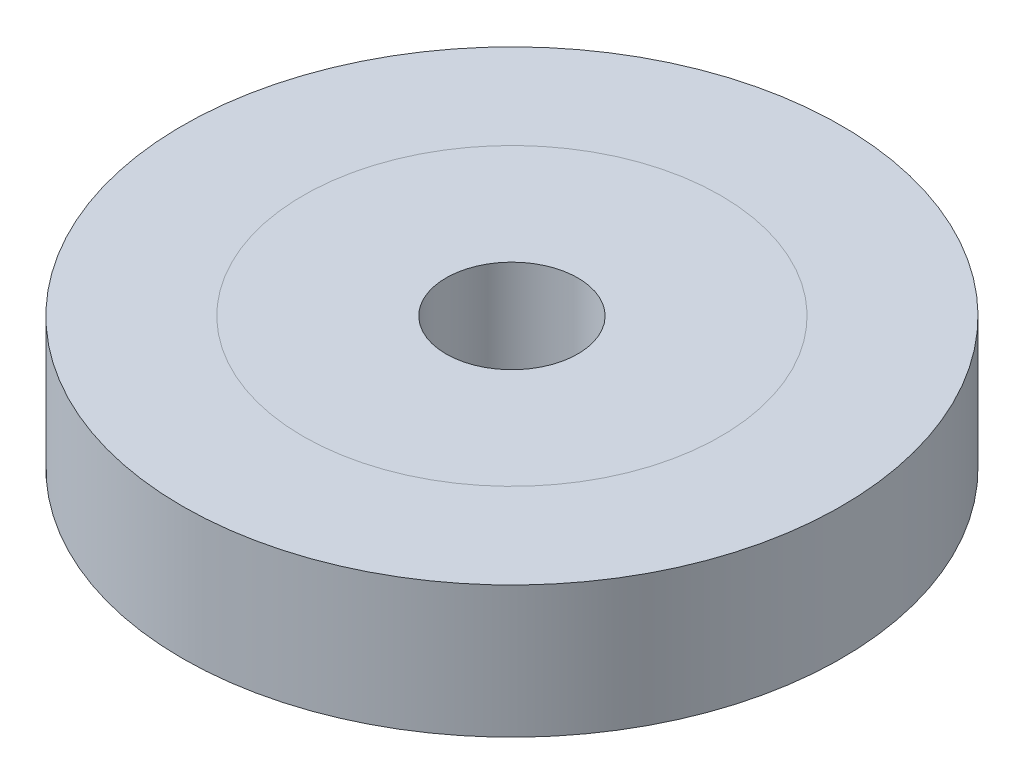
SolidWorks part; units mm, degrees
ref_plane "前视基准面" through (0, 0, 0) normal (0, 0, 1) x (1, 0, 0)
ref_plane "上视基准面" through (0, 0, 0) normal (0, 1, 0) x (1, 0, 0)
ref_plane "右视基准面" through (0, 0, 0) normal (1, 0, 0) x (0, 0, -1)
sketch "草图1" plane through (0, 0, 0) normal (0, 1, 0) x (1, 0, 0)
  circle A0 centre (0, 0) radius 3
  circle A1 centre (0, 0) radius 9.5
  dimension "D1" = 6
  dimension "D2" = 19
extrude "凸台-拉伸1" add sketch "草图1" along normal mid plane 6
sketch "草图2" plane through (0, 0, 0) normal (0, 1, 0) x (1, 0, 0)
  circle A0 centre (0, 0) radius 15
  circle A1 centre (0, 0) radius 9.5 construction
  circle A2 centre (0, 0) radius 9.5
  dimension "D1" = 30
extrude "凸台-拉伸2" add sketch "草图2" along normal mid plane 6 separate body
sketch "草图3" plane through (0, 3, 0) normal (0, 1, 0) x (1, 0, 0)
  circle A2 centre (0, 0) radius 14.5
  circle A3 centre (0, 0) radius 14.5 construction
  text T0 "https://item.taobao.com/item.htm?spm=a1z10.3-c.w4002-15226105362.54.3c39319dTIL82A&id=599558765708" font "黑体" height 1
  dimension "D1" = 0.5
extrude "切除-拉伸1" [suppressed] cut sketch "草图3" against normal blind 0.1
